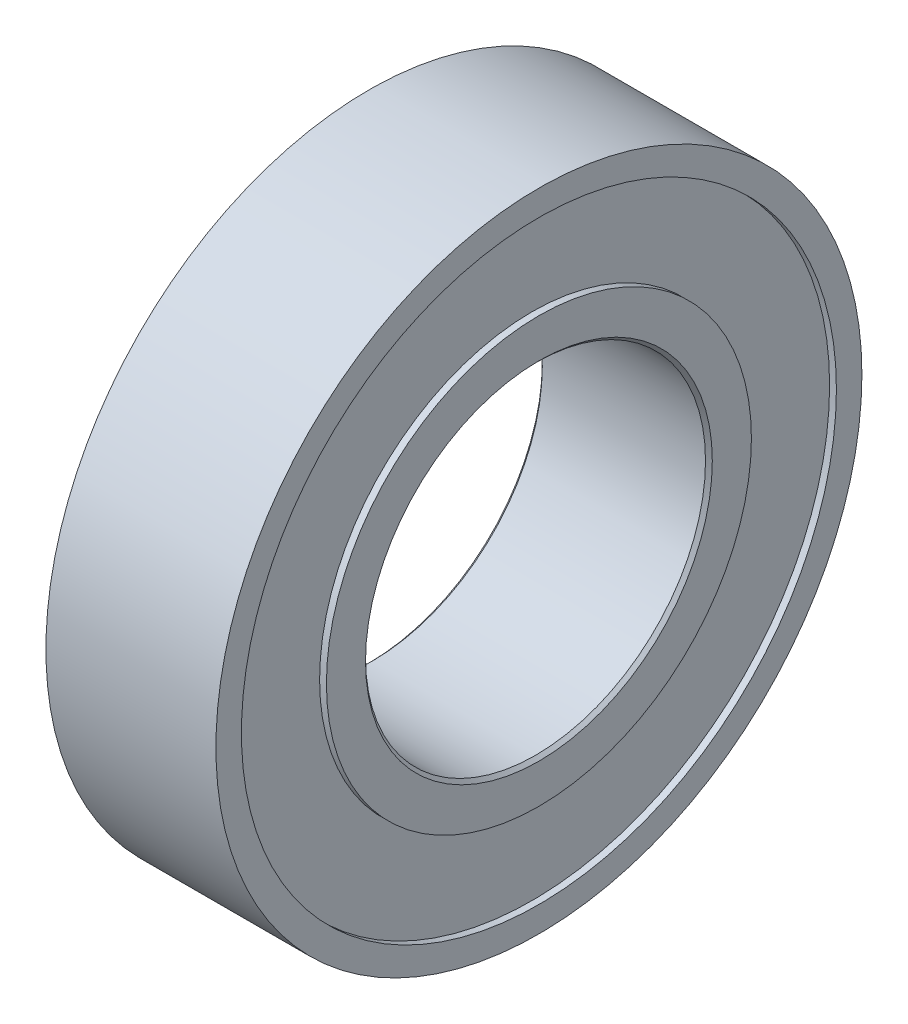
SolidWorks part; units mm, degrees
ref_plane "前视基准面" through (0, 0, 0) normal (0, 0, 1) x (1, 0, 0)
ref_plane "上视基准面" through (0, 0, 0) normal (0, 1, 0) x (1, 0, 0)
ref_plane "右视基准面" through (0, 0, 0) normal (1, 0, 0) x (0, 0, -1)
sketch "草图1" plane through (0, 0, 0) normal (1, 0, 0) x (0, 0, -1)
  circle A0 centre (0, 0) radius 5
  circle A1 centre (0, 0) radius 9.5
  dimension "D1" = 10
  dimension "D2" = 19
extrude "凸台-拉伸1" add sketch "草图1" along normal blind 5
sketch "草图2" plane through (0, 0, 0) normal (-1, 0, 0) x (0, 0, 1)
  circle A0 centre (0.1116, 0) radius 6.25
  circle A1 centre (0.1116, 0) radius 8.25
  dimension "D1" = 12.5
  dimension "D2" = 16.5
extrude "切除-拉伸1" cut sketch "草图2" against normal blind 0.2
sketch "草图3" plane through (5, 0, 0) normal (1, 0, 0) x (0, 0, -1)
  circle A0 centre (0, 0) radius 6.25
  circle A1 centre (0, 0) radius 8.75
  dimension "D1" = 12.5
  dimension "D2" = 17.5
extrude "切除-拉伸2" cut sketch "草图3" against normal blind 0.2
chamfer "倒角2" distance 0.1 angle 45 2 edges at (0, 0, -5) (5, 0, -5)
